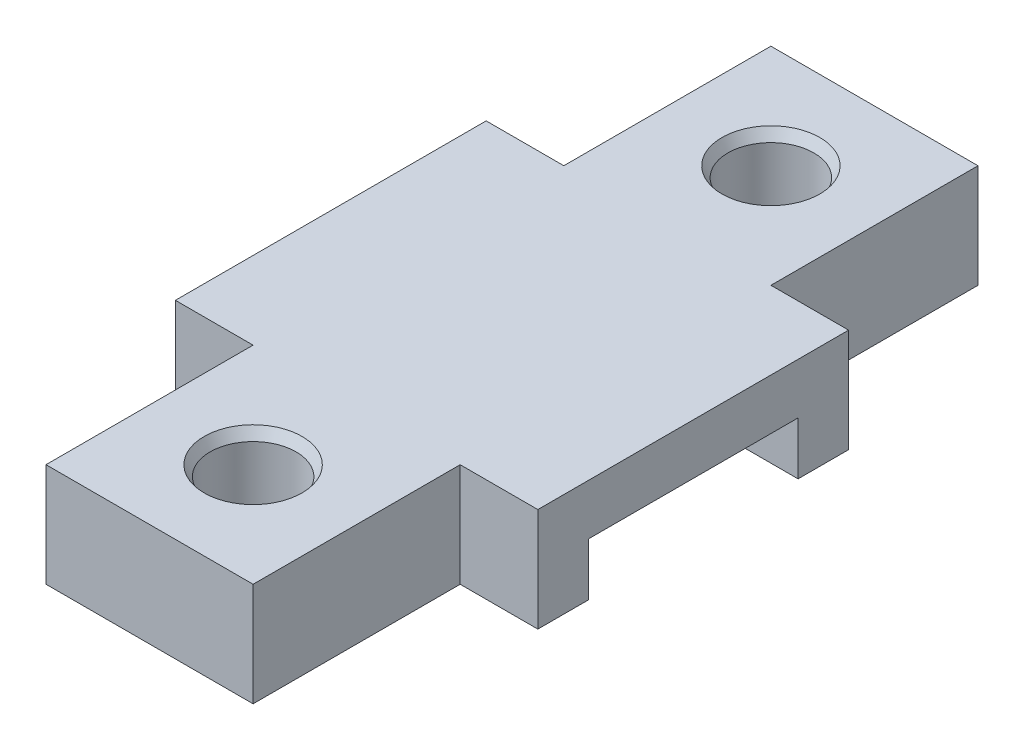
SolidWorks part; units mm, degrees
ref_plane "Спереди" through (0, 0, 0) normal (0, 0, 1) x (1, 0, 0)
ref_plane "Сверху" through (0, 0, 0) normal (0, 1, 0) x (1, 0, 0)
ref_plane "Справа" through (0, 0, 0) normal (1, 0, 0) x (0, 0, -1)
sketch "Sketch1" plane through (0, 0, 0) normal (0, 1, 0) x (1, 0, 0)
  line L1 (10, -35) -> (-10, -35)
  line L2 (10, -35) -> (10, 35)
  line L3 (10, 35) -> (-10, 35)
  line L4 (-10, -35) -> (-10, 35)
  line L5 (10, -35) -> (-10, 35) construction
  line L6 (10, 35) -> (-10, -35) construction
  point P0 (0, 0)
  dimension "D1" = 20
  dimension "D2" = 70
extrude "Boss-Extrude1" add sketch "Sketch1" along normal blind 10
sketch "Sketch2" plane through (10, 0, 0) normal (1, 0, 0) x (0, 0, -1)
  line L0 (0, 0) -> (0, 10) construction
  line L1 (-35, 0) -> (35, 0) construction
  line L2 (-35, 10) -> (35, 10) construction
  line L4 (10.125, 5.1) -> (-10.125, 5.1)
  line L5 (10.125, 5.1) -> (10.125, 0)
  line L6 (10.125, 0) -> (-10.125, 0)
  line L7 (-10.125, 5.1) -> (-10.125, 0)
  line L8 (10.125, 5.1) -> (-10.125, 0) construction
  line L9 (10.125, 0) -> (-10.125, 5.1) construction
  point P6 (0, 2.55)
  dimension "D1" = 20.25
  dimension "D2" = 5.1
extrude "Cut-Extrude1" cut sketch "Sketch2" against normal through all and the other way through all
sketch "Sketch3" plane through (0, 0, 0) normal (0, -1, 0) x (1, 0, 0)
  line L0 (0, 35) -> (0, -35) construction
  line L1 (-10, 35) -> (10, 35) construction
  line L2 (10, -35) -> (-10, -35) construction
  circle A0 centre (0, 25) radius 4.15
  circle A1 centre (0, -25) radius 4.15
  dimension "D1" = 8.3
  dimension "D2" = 25
  dimension "D3" = 50
extrude "Cut-Extrude2" cut sketch "Sketch3" against normal through all
sketch "Sketch4" plane through (10, 0, 0) normal (1, 0, 0) x (0, 0, -1)
  line L0 (-10.125, 0) -> (-15.005, 0)
  line L1 (-35, 0) -> (-10.125, 0) construction
  line L2 (-15.005, 0) -> (-15.005, 10)
  line L3 (-35, 10) -> (35, 10) construction
  line L4 (-15.005, 10) -> (15.005, 10)
  line L5 (15.005, 10) -> (15.005, 0)
  line L6 (10.125, 0) -> (35, 0) construction
  line L7 (15.005, 0) -> (10.125, 0)
  line L8 (10.125, 0) -> (10.125, 5.1)
  line L9 (10.125, 5.1) -> (-10.125, 5.1)
  line L10 (-10.125, 5.1) -> (-10.125, 0)
  dimension "D1" = 4.88
extrude "Boss-Extrude2" add sketch "Sketch4" along normal blind 7.5 and the other way blind 27.5
chamfer "Chamfer1" distance 1 angle 30 2 edges at (0, 10, -29.15) (0, 10, 20.85)
